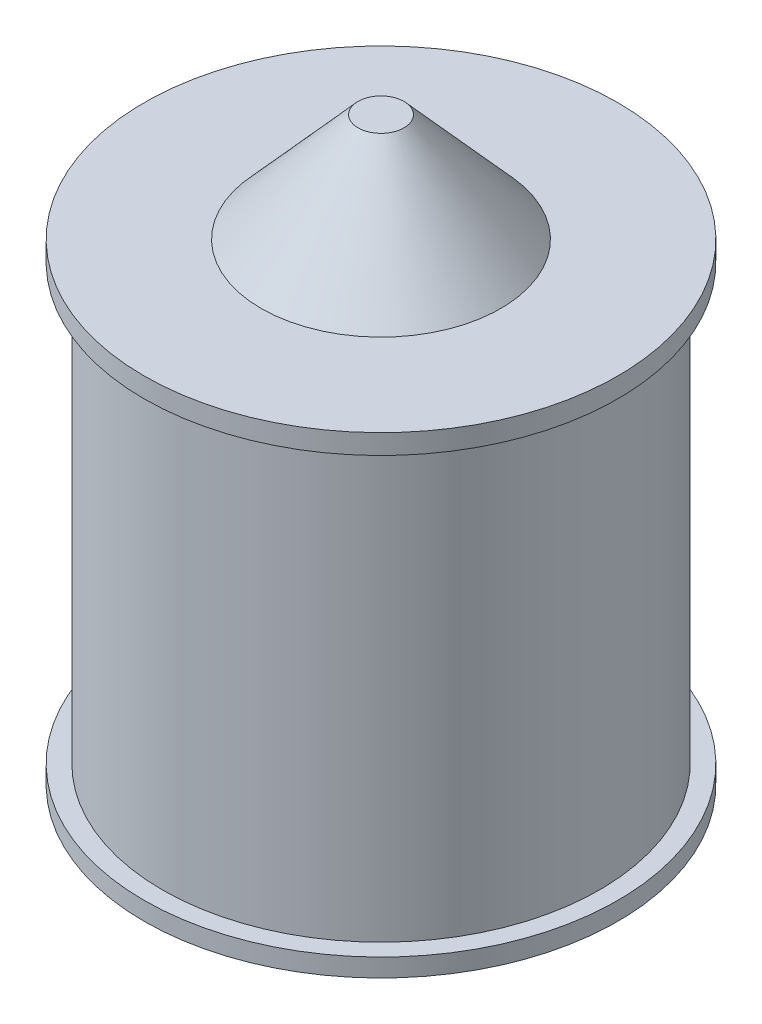
SolidWorks part; units mm, degrees
ref_plane "Alzado" through (0, 0, 0) normal (0, 0, 1) x (1, 0, 0)
ref_plane "Planta" through (0, 0, 0) normal (0, 1, 0) x (1, 0, 0)
ref_plane "Vista lateral" through (0, 0, 0) normal (1, 0, 0) x (0, 0, -1)
sketch "Croquis1" plane through (0, 0, 0) normal (0, 0, 1) x (1, 0, 0)
  line L0 (0, 38.8006) -> (0, -62.5731)
  line L1 (0, -62.5731) -> (50.8215, -62.5731)
  line L2 (50.8215, -62.5731) -> (50.8215, -58.6741)
  line L3 (50.8215, -58.6741) -> (46.9225, -58.6741)
  line L4 (46.9225, -58.6741) -> (46.9225, 34.5472)
  line L5 (46.9225, 34.5472) -> (50.8215, 34.5472)
  line L6 (50.8215, 34.5472) -> (50.8215, 38.8006)
  line L7 (50.8215, 38.8006) -> (0, 38.8006)
  dimension "D7" = 4.2534
  dimension "D1" = 101.3738
  dimension "D2" = 50.8215
  dimension "D3" = 3.899
  dimension "D4" = 3.899
  dimension "D5" = 93.2213
  dimension "D6" = 3.899
  dimension "D8" = 50.8215
revolve "Revolución1" add sketch "Croquis1" angle 360 about L0
ref_plane "Plano1" through (0, 0, 0) normal (0, 0, 1) x (1, 0, 0)
sketch "Croquis3" plane through (0, 0, 0) normal (0, 0, 1) x (1, 0, 0)
  line L0 (50.8215, -58.6741) -> (-50.8215, -58.6741) construction
  line L1 (-46.8969, 34.5263) -> (-44.3969, 34.5263)
  line L2 (-46.8969, 34.5263) -> (-46.8969, -58.6741)
  line L3 (-46.8969, -58.6741) -> (-44.3969, -58.6741)
  line L4 (-44.3969, 34.5263) -> (-44.3969, -58.6741)
  line L5 (-46.9225, 34.5472) -> (46.9225, 34.5472) construction
  line L6 (-41.3745, 34.5472) -> (-38.8745, 34.5472)
  line L7 (-41.3745, 34.5472) -> (-41.3745, -58.6741)
  line L8 (-41.3745, -58.6741) -> (-38.8745, -58.6741)
  line L9 (-38.8745, 34.5472) -> (-38.8745, -58.6741)
  dimension "D1" = 2.5
  dimension "D2" = 2.5
extrude "Saliente-Extruir1" add sketch "Croquis3" against normal blind 25 draft 1
sketch "Croquis5" plane through (0, 0, 0) normal (0, 0, 1) x (1, 0, 0)
  line L0 (0, 61.9733) -> (0, -94.3216) construction
  dimension "D1" = 156.2948
ref_plane "Plano2" through (0, 0, 0) normal (0, 0, 1) x (1, 0, 0)
sketch "Croquis6" plane through (0, 0, 0) normal (0, 0, 1) x (1, 0, 0)
  line L0 (37.4287, 61.7075) -> (37.4287, -71.7758) construction
  line L1 (-30.9408, 61.7075) -> (-30.9408, -75.0315) construction
  line L2 (0, 61.9733) -> (0, -94.3216) construction
  line L3 (0, 61.9733) -> (0, 34.5472)
  line L4 (-46.9225, 34.5472) -> (46.9225, 34.5472) construction
  line L5 (0, 34.5472) -> (-30.9408, 34.5472)
  line L6 (-30.9408, 34.5472) -> (-30.9408, 38.8006)
  line L7 (50.8215, 38.8006) -> (-50.8215, 38.8006) construction
  line L8 (-25.7229, 38.8006) -> (-4.9247, 61.9733)
  line L9 (-4.9247, 61.9733) -> (0, 61.9733)
  line L10 (-25.7229, 38.8006) -> (-30.9408, 38.8006)
  dimension "D1" = 133.4833
  dimension "D2" = 136.739
revolve "Revolución2" add sketch "Croquis6" angle 360 about L3
